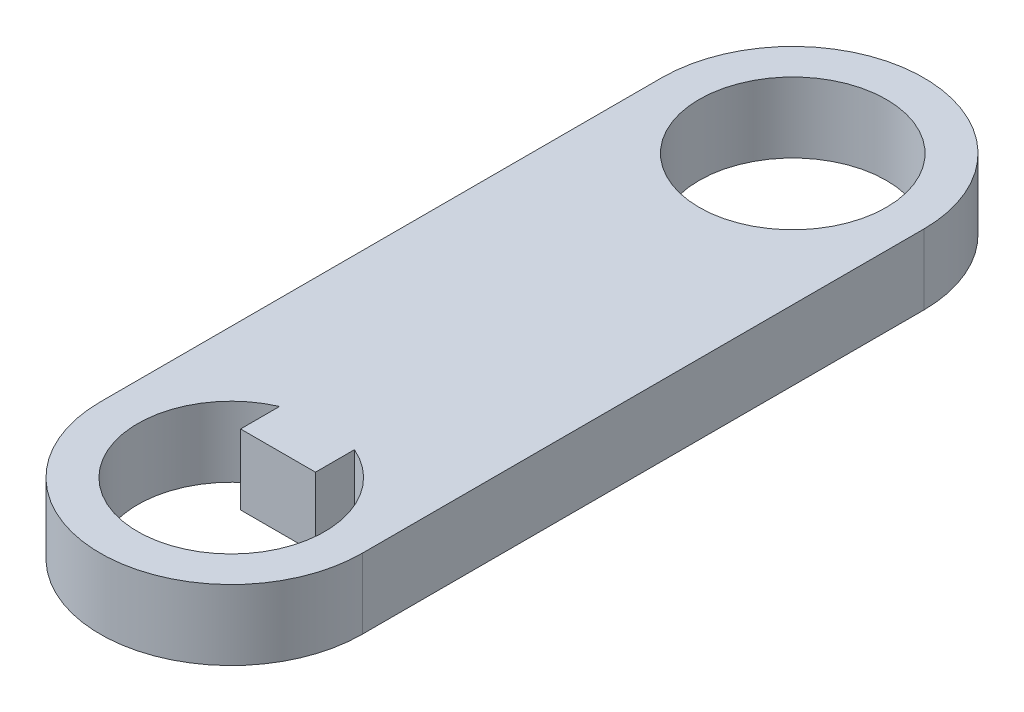
SolidWorks part; units mm, degrees
ref_plane "Front Plane" through (0, 0, 0) normal (0, 0, 1) x (1, 0, 0)
ref_plane "Top Plane" through (0, 0, 0) normal (0, 1, 0) x (1, 0, 0)
ref_plane "Right Plane" through (0, 0, 0) normal (1, 0, 0) x (0, 0, -1)
sketch "Sketch1" plane through (0, 0, 0) normal (0, 1, 0) x (1, 0, 0)
  line L0 (0, 60) -> (0, 0) construction
  line L1 (14, 60) -> (14, 0)
  line L2 (-14, 60) -> (-14, 0)
  line L4 (4, 5) -> (-4, 5)
  line L5 (4, 5) -> (4, 15)
  line L6 (4, 15) -> (-4, 15)
  line L7 (-4, 5) -> (-4, 15)
  line L8 (4, 5) -> (-4, 15) construction
  line L9 (4, 15) -> (-4, 5) construction
  arc A0 (14, 60) -> (-14, 60) centre (0, 60) ccw
  arc A1 (-14, 0) -> (14, 0) centre (0, 0) ccw
  circle A2 centre (0, 0) radius 10
  circle A3 centre (0, 60) radius 10
  point P2 (0, 30)
  point P9 (0, 10)
  dimension "D1" = 20
  dimension "D2" = 20
  dimension "D4" = 14
  dimension "D3" = 60
  dimension "D5" = 8
  dimension "D6" = 10
extrude "Boss-Extrude1" add sketch "Sketch1" along normal blind 7.5 contours L2 A1 L1 A0 A3 A2 L7 L6 L5
equation "\"shaftDiam\" = 20mm"
equation "\"keyW\" = 8mm"
equation "\"keyL\" = 10mm"
equation "\"clearance\" = 1mm"
equation "\"handleShaftLen\" = 60mm"
equation "\"D1@Sketch1\"=\"shaftDiam\""
equation "\"D2@Sketch1\"=\"shaftDiam\""
equation "\"D3@Sketch1\"=\"handleShaftLen\""
equation "\"D4@Sketch1\"=\"shaftDiam\"*.7"
equation "\"D5@Sketch1\"=\"keyW\""
equation "\"D6@Sketch1\"=\"keyL\""
equation "\"D1@Boss-Extrude1\"=\"handleShaftLen\"/8"
